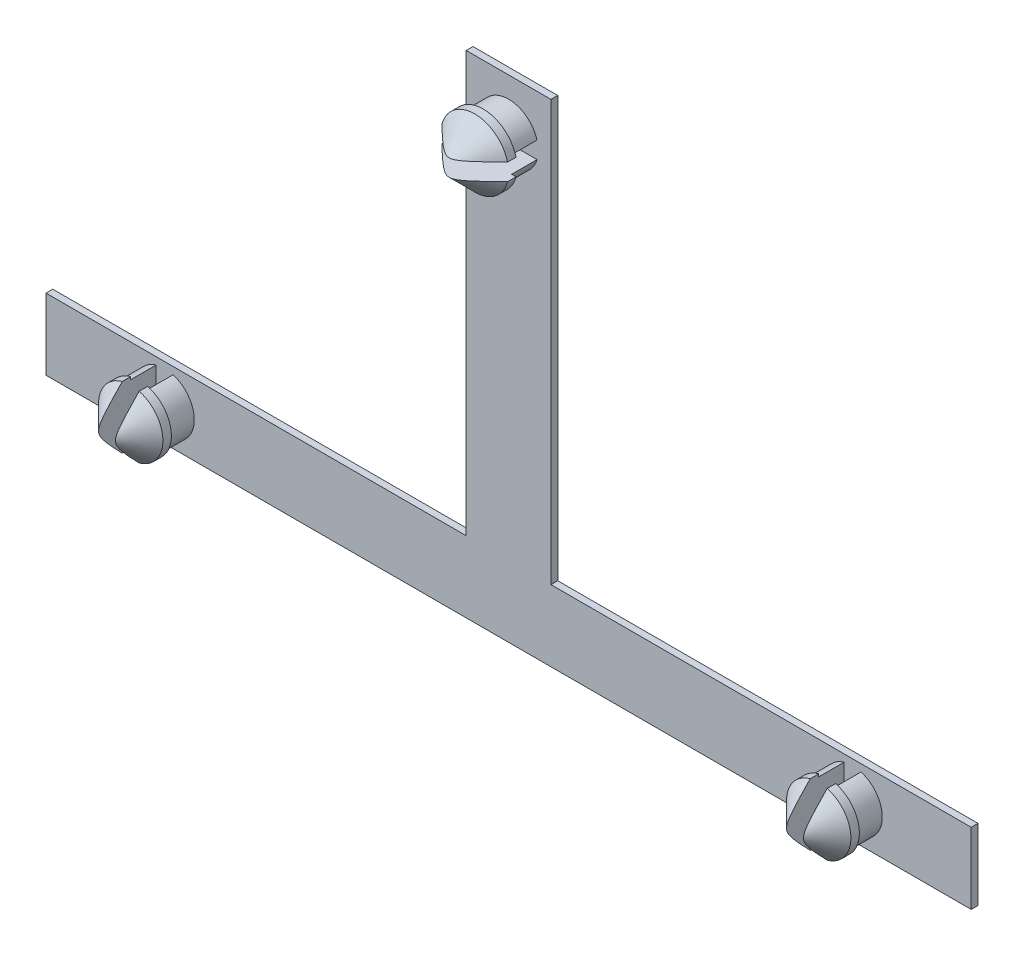
SolidWorks part; units mm, degrees
ref_plane "Přední rovina" through (0, 0, 0) normal (0, 0, 1) x (1, 0, 0)
ref_plane "Horní rovina" through (0, 0, 0) normal (0, 1, 0) x (1, 0, 0)
ref_plane "Pravá rovina" through (0, 0, 0) normal (1, 0, 0) x (0, 0, -1)
sketch "Skica2" plane through (0, 0, 0) normal (0, 0, 1) x (1, 0, 0)
  line L1 (-27.3, 2.1) -> (27.3, 2.1)
  line L2 (-27.3, 2.1) -> (-27.3, -2.1)
  line L3 (-27.3, -2.1) -> (27.3, -2.1)
  line L4 (27.3, 2.1) -> (27.3, -2.1)
  line L5 (-27.3, 2.1) -> (27.3, -2.1) construction
  line L6 (-27.3, -2.1) -> (27.3, 2.1) construction
  point P0 (0, 0)
  point P5 (-1, -0.2)
  dimension "D1" = 4.2
  dimension "D2" = 54.6
extrude "Přidat vysunutím2" add sketch "Skica2" along normal blind 0.4
sketch "Skica3" plane through (0, 0, 0.4) normal (0, 0, 1) x (1, 0, 0)
  line L0 (-27.3, 2.1) -> (-27.3, -2.1) construction
  line L1 (27.3, -2.1) -> (27.3, 2.1) construction
  line L2 (27.3, 2.1) -> (-27.3, 2.1) construction
  line L3 (-27.3, -2.1) -> (27.3, -2.1) construction
  circle A0 centre (-20.3, 0) radius 1.75
  circle A1 centre (20.3, 0) radius 1.75
  dimension "D1" = 3.5
  dimension "D3" = 3.5
  dimension "D2" = 7
  dimension "D4" = 7
  dimension "D5" = 2.1
  dimension "D6" = 2.1
extrude "Přidat vysunutím3" add sketch "Skica3" along normal blind 1.5
sketch "Skica5" plane through (0, 0, 1.9) normal (0, 0, 1) x (1, 0, 0)
  circle A0 centre (-20.3, 0) radius 1.9
  circle A1 centre (20.3, 0) radius 1.9
  dimension "D1" = 3.8
  dimension "D2" = 3.8
extrude "Přidat vysunutím5" add sketch "Skica5" along normal blind 2
chamfer "Zkosení2" distance 1.5 angle 45 2 edges at (22.2, 0, 3.9) (-18.4, 0, 3.9)
sketch "Skica7" plane through (0, 0, 3.9) normal (0, 0, 1) x (1, 0, 0)
  line L1 (-19.8, 2.5) -> (-20.8, 2.5)
  line L2 (-19.8, 2.5) -> (-19.8, -2.5)
  line L3 (-19.8, -2.5) -> (-20.8, -2.5)
  line L4 (-20.8, 2.5) -> (-20.8, -2.5)
  line L5 (-19.8, 2.5) -> (-20.8, -2.5) construction
  line L6 (-19.8, -2.5) -> (-20.8, 2.5) construction
  line L7 (19.8, 2.5) -> (20.8, 2.5)
  line L8 (19.8, 2.5) -> (19.8, -2.5)
  line L9 (19.8, -2.5) -> (20.8, -2.5)
  line L10 (20.8, 2.5) -> (20.8, -2.5)
  line L11 (19.8, 2.5) -> (20.8, -2.5) construction
  line L12 (19.8, -2.5) -> (20.8, 2.5) construction
  point P0 (-20.3, 0)
  point P5 (20.3, 0)
  dimension "D1" = 5
  dimension "D2" = 1
  dimension "D3" = 5
  dimension "D4" = 1
extrude "Odebrat vysunutím1" cut sketch "Skica7" against normal blind 3.5
sketch "Skica8" plane through (0, 0, 0) normal (0, 0, -1) x (-1, 0, 0)
  line L0 (-27.3, 2.1) -> (27.3, 2.1) construction
  line L1 (2.5, 2.1) -> (-2.5, 2.1)
  line L2 (2.5, 2.1) -> (2.5, 26.9)
  line L3 (2.5, 26.9) -> (-2.5, 26.9)
  line L4 (-2.5, 2.1) -> (-2.5, 26.9)
  line L5 (27.3, 2.1) -> (27.3, -2.1) construction
  dimension "D1" = 24.8
  dimension "D2" = 5
  dimension "D3" = 24.8
extrude "Přidat vysunutím6" add sketch "Skica8" against normal blind 0.4
sketch "Skica9" plane through (0, 0, 0.4) normal (0, 0, 1) x (1, 0, 0)
  circle A0 centre (0, 23.9107) radius 1.75
  dimension "D1" = 3.5
extrude "Přidat vysunutím7" add sketch "Skica9" along normal blind 1.5
sketch "Skica10" plane through (0, 0, 1.9) normal (0, 0, 1) x (1, 0, 0)
  circle A0 centre (0, 23.9107) radius 2
  dimension "D1" = 4
extrude "Přidat vysunutím8" add sketch "Skica10" along normal blind 2
chamfer "Zkosení3" distance 1.5 angle 45 1 edges at (2, 23.9107, 3.9)
sketch "Skica11" plane through (0, 0, 3.9) normal (0, 0, 1) x (1, 0, 0)
  line L0 (-2.5, 2.1) -> (-2.5, 26.9) construction
  line L1 (2.5, 24.4107) -> (-2.5, 24.4107)
  line L2 (2.5, 24.4107) -> (2.5, 23.4107)
  line L3 (2.5, 23.4107) -> (-2.5, 23.4107)
  line L4 (-2.5, 24.4107) -> (-2.5, 23.4107)
  line L5 (2.5, 24.4107) -> (-2.5, 23.4107) construction
  line L6 (2.5, 23.4107) -> (-2.5, 24.4107) construction
  point P0 (0, 23.9107)
extrude "Odebrat vysunutím2" cut sketch "Skica11" against normal blind 3.5
equation "\"1.5.000mm\"=10"
